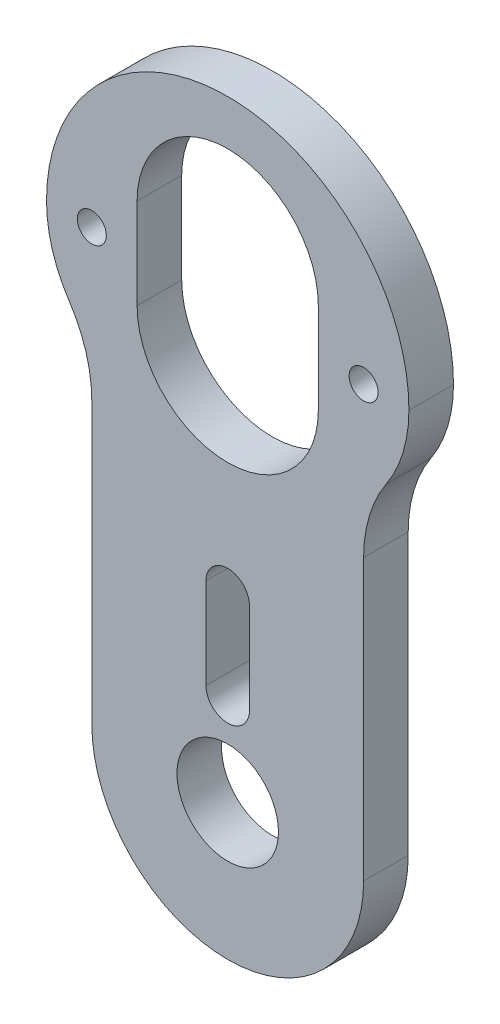
SolidWorks part; units mm, degrees
ref_plane "Alzado" through (0, 0, 0) normal (0, 0, 1) x (1, 0, 0)
ref_plane "Planta" through (0, 0, 0) normal (0, 1, 0) x (1, 0, 0)
ref_plane "Vista lateral" through (0, 0, 0) normal (1, 0, 0) x (0, 0, -1)
sketch "Croquis1" plane through (0, 0, 0) normal (0, 0, 1) x (1, 0, 0)
  line L0 (0, 0) -> (0, 33.3375) construction
  line L3 (-9.525, 0) -> (-9.525, 33.3375)
  line L6 (9.525, 0) -> (9.525, 33.3375)
  line L9 (0, 6.35) -> (0, 12.7) construction
  line L10 (-1.524, 6.35) -> (-1.524, 12.7)
  line L11 (1.524, 6.35) -> (1.524, 12.7)
  line L12 (0, 33.3375) -> (0, 26.9875) construction
  line L13 (6.35, 33.3375) -> (6.35, 26.9875)
  line L14 (-6.35, 33.3375) -> (-6.35, 26.9875)
  arc A8 (-9.525, 0) -> (9.525, 0) centre (0, 0) ccw
  arc A9 (9.525, 33.3375) -> (-9.525, 33.3375) centre (0, 33.3375) ccw
  circle A10 centre (0, 0) radius 3.556
  arc A11 (-1.524, 6.35) -> (1.524, 6.35) centre (0, 6.35) ccw
  arc A12 (1.524, 12.7) -> (-1.524, 12.7) centre (0, 12.7) ccw
  arc A13 (6.35, 33.3375) -> (-6.35, 33.3375) centre (0, 33.3375) ccw
  arc A14 (-6.35, 26.9875) -> (6.35, 26.9875) centre (0, 26.9875) ccw
  circle A15 centre (0, 30.1625) radius 6.35
  point P2 (0, 16.6687)
  point P12 (0, 9.525)
  point P17 (0, 30.1625)
  dimension "D2" = 6.35
  dimension "D1" = 6.35
  dimension "D3" = 3.048
  dimension "D4" = 7.112
  dimension "D7" = 9.525
  dimension "D5" = 6.35
  dimension "D6" = 26.9875
  dimension "D8" = 12.7
  dimension "D9" = 3.175
extrude "Saliente-Extruir1" add sketch "Croquis1" along normal blind 3.1242 contours L6 A9 L3 A8 A14 L14 A13 L13 A12 L11 A11 L10 A10
sketch "Croquis2" plane through (0, 0, 3.1242) normal (0, 0, 1) x (1, 0, 0)
  line L0 (0, 33.3375) -> (0, 26.9875) construction
  line L1 (-3.175, 30.1625) -> (3.175, 30.1625) construction
  line L2 (-3.175, 39.6875) -> (3.175, 39.6875)
  line L3 (-3.175, 20.6375) -> (3.175, 20.6375)
  line L4 (-9.525, 0) -> (-9.525, 33.3375) construction
  line L5 (9.525, 0) -> (9.525, 33.3375) construction
  circle A0 centre (0, 33.3375) radius 6.35
  circle A1 centre (0, 26.9875) radius 6.35
  arc A2 (6.35, 33.3375) -> (-6.35, 33.3375) centre (0, 33.3375) ccw construction
  arc A3 (-3.175, 39.6875) -> (-3.175, 20.6375) centre (-3.175, 30.1625) ccw
  arc A4 (3.175, 20.6375) -> (3.175, 39.6875) centre (3.175, 30.1625) ccw
  arc A5 (-12.7, 30.1625) -> (0, 42.8625) centre (0, 30.1625) cw
  arc A6 (9.525, 33.3375) -> (-9.525, 33.3375) centre (0, 33.3375) ccw construction
  arc A7 (0, 42.8625) -> (12.7, 30.1625) centre (0, 30.1625) cw
  arc A8 (-11.1125, 24.8974) -> (-9.525, 19.6322) centre (-19.05, 19.6322) cw
  arc A9 (11.1125, 24.8974) -> (9.525, 19.6322) centre (19.05, 19.6322) ccw
  circle A10 centre (-9.525, 30.1625) radius 1.016
  circle A11 centre (9.525, 30.1625) radius 1.016
  circle A12 centre (9.525, 30.1625) radius 1.016
  point P12 (0, 30.1625)
  point P37 (-5.4993, 30.1625)
  point P38 (0, 0)
  point P42 (0, 0)
  point P43 (0, 0)
  point P44 (-2.8995, 30.1625)
  point P45 (0, 0)
  arc M5 (6.35, 26.9875) -> (-6.35, 26.9875) centre (0, 26.9875) cw
  arc M7 (-6.35, 33.3375) -> (6.35, 33.3375) centre (0, 33.3375) cw
  line M8 (6.35, 33.3375) -> (6.35, 26.9875)
  line M14 (9.525, 0) -> (9.525, 33.3375)
  arc M15 (9.525, 33.3375) -> (-9.525, 33.3375) centre (0, 33.3375) ccw
  line M16 (-9.525, 33.3375) -> (-9.525, 0)
  dimension "D1" = 9.525
  dimension "D2" = 2.032
  dimension "D3" = 6.35
extrude "Saliente-Extruir3" add sketch "Croquis2" against normal blind 3.1242 contours A7 A4 M15 | A4 A3 L2 M15 | A5 A3 M15 | A3 A10 M15 M16 | A4 A11 M14 M15 | A9 A4 M14 | A3 A8 M16 | A4 L2 L3 M15 M7 M8 M5 M14
sketch "Croquis3" plane through (0, 0, 3.1242) normal (0, 0, 1) x (1, 0, 0)
  circle A0 centre (-9.525, 30.1625) radius 1.016
  circle A1 centre (9.525, 30.1625) radius 1.016
  circle A2 centre (-9.525, 30.1625) radius 1.016 construction
  circle A3 centre (9.525, 30.1625) radius 1.016 construction
extrude "Cortar-Extruir1" cut sketch "Croquis3" against normal through all
